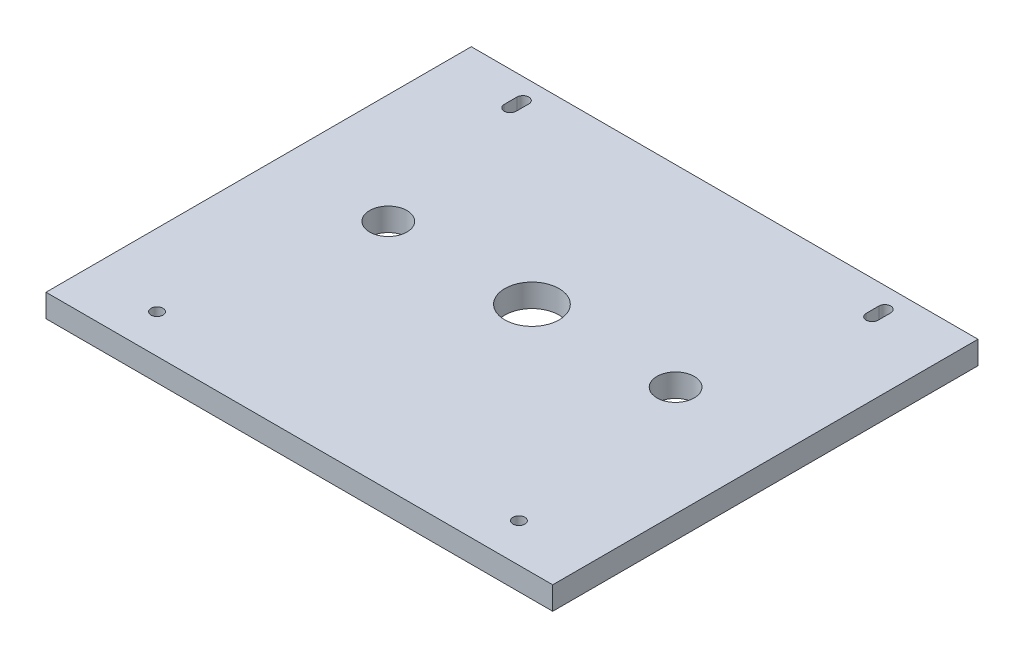
SolidWorks part; units mm, degrees
ref_plane "Front Plane" through (0, 0, 0) normal (0, 0, 1) x (1, 0, 0)
ref_plane "Top Plane" through (0, 0, 0) normal (0, 1, 0) x (1, 0, 0)
ref_plane "Right Plane" through (0, 0, 0) normal (1, 0, 0) x (0, 0, -1)
sketch "Sketch1" plane through (0, 0, 0) normal (0, 1, 0) x (1, 0, 0)
  line L1 (0, 0) -> (140, 0)
  line L2 (0, 0) -> (0, 117.505)
  line L3 (0, 117.505) -> (140, 117.505)
  line L4 (140, 0) -> (140, 117.505)
  dimension "D1" = 117.505
  dimension "D2" = 140
extrude "Boss-Extrude1" add sketch "Sketch1" along normal blind 6.35
sketch "Sketch2" plane through (0, 6.35, 0) normal (0, 1, 0) x (1, 0, 0)
  line L1 (0, 117.505) -> (0, 0) construction
  line L2 (140, 0) -> (140, 117.505) construction
  line L3 (70, 117.505) -> (70, 0) construction
  line L4 (140, 117.505) -> (0, 117.505) construction
  line L5 (0, 0) -> (140, 0) construction
  line L6 (0, 10.675) -> (140, 10.675) construction
  line L7 (0, 110.005) -> (140, 110.005) construction
  line L8 (120, 108.255) -> (120, 111.755) construction
  line L11 (20, 108.255) -> (20, 111.755) construction
  line L12 (18.35, 108.255) -> (18.35, 111.755)
  line L13 (21.65, 108.255) -> (21.65, 111.755)
  line L14 (121.65, 108.255) -> (121.65, 111.755)
  line L17 (118.35, 108.255) -> (118.35, 111.755)
  circle A0 centre (20, 10.675) radius 1.65
  arc A6 (18.35, 108.255) -> (21.65, 108.255) centre (20, 108.255) ccw
  arc A7 (21.65, 111.755) -> (18.35, 111.755) centre (20, 111.755) ccw
  circle A12 centre (70, 64.265) radius 7.5
  circle A15 centre (30.3125, 64.265) radius 5.16
  circle A16 centre (120, 10.675) radius 1.65
  circle A17 centre (109.6875, 64.265) radius 5.16
  arc A18 (121.65, 108.255) -> (118.35, 108.255) centre (120, 108.255) cw
  arc A19 (118.35, 111.755) -> (121.65, 111.755) centre (120, 111.755) cw
  point P0 (109.3502, 64.2807)
  point P26 (120, 110.005)
  point P33 (20, 110.005)
  point P38 (131.627, 59.1175)
  point P39 (10.2431, 59.1175)
  dimension "D5" = 3.3
  dimension "D10" = 15
  dimension "D8" = 10.32
  dimension "D2" = 45.74
  dimension "D3" = 50
  dimension "D4" = 50
  dimension "D6" = 3.3
  dimension "D7" = 3.5
  dimension "D9" = 39.6875
  dimension "D11" = 10.675
  dimension "D13" = 53.59
extrude "Cut-Extrude1" cut sketch "Sketch2" against normal through all
